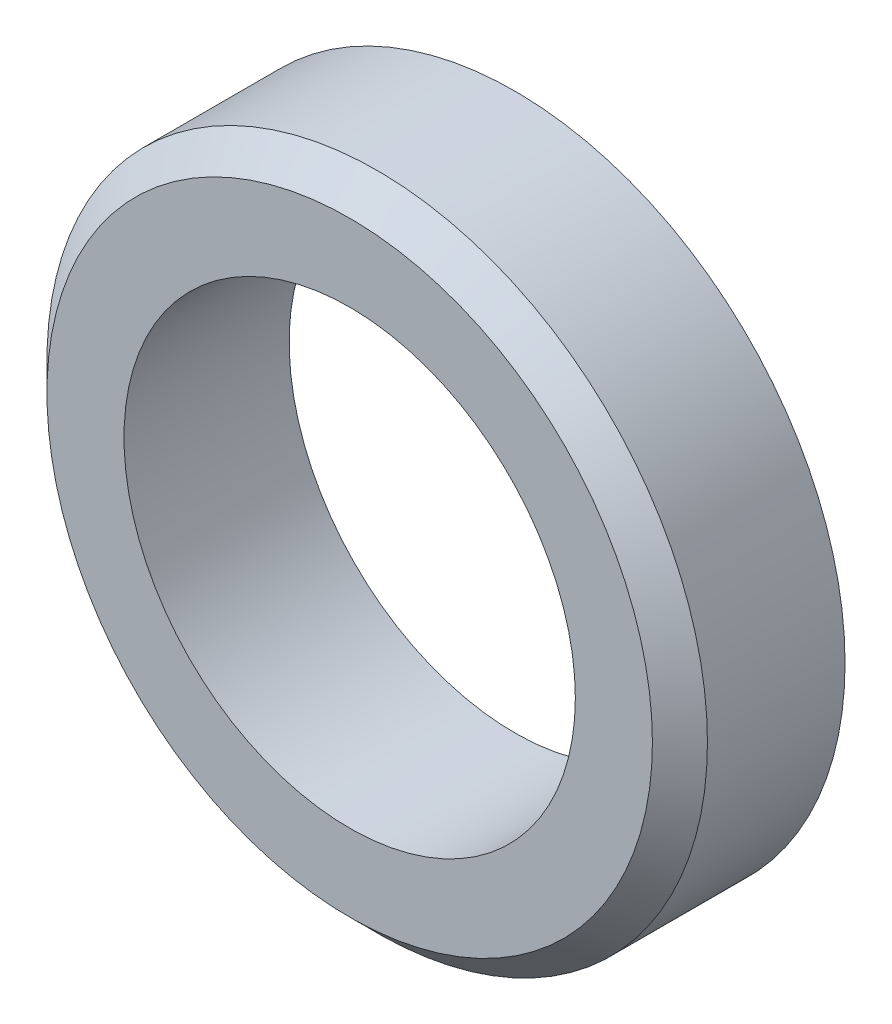
SolidWorks part; units mm, degrees
material "3.1325 (EN-AW 2017A)"
ref_plane "Plan de face" through (0, 0, 0) normal (0, 0, 1) x (1, 0, 0)
ref_plane "Plan de dessus" through (0, 0, 0) normal (0, 1, 0) x (1, 0, 0)
ref_plane "Plan de droite" through (0, 0, 0) normal (1, 0, 0) x (0, 0, -1)
sketch "Esquisse1" plane through (0, 0, 0) normal (0, 0, 1) x (1, 0, 0)
  circle A0 centre (0, 0) radius 6
extrude "Boss.-Extru.1" add sketch "Esquisse1" along normal blind 3
sketch "Esquisse2" plane through (0, 0, 3) normal (0, 0, 1) x (1, 0, 0)
  circle A0 centre (0, 0) radius 4.1
extrude "Enlèv. mat.-Extru.1" cut sketch "Esquisse2" against normal through all
chamfer "Chanfrein1" distance 0.5 angle 45 1 edges at (6, 0, 3)
